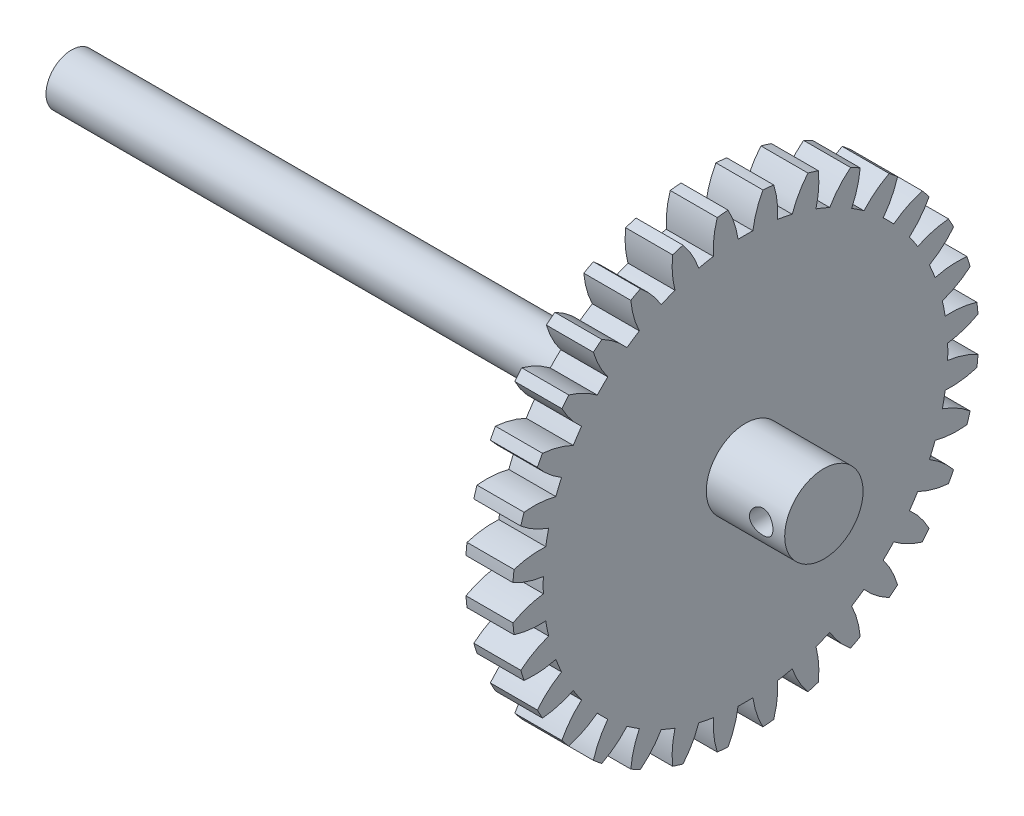
SolidWorks part; units mm, degrees
ref_plane "Plane1" through (0, 0, 0) normal (0, 0, 1) x (1, 0, 0)
ref_plane "Plane2" through (0, 0, 0) normal (0, 1, 0) x (1, 0, 0)
ref_plane "Plane3" through (0, 0, 0) normal (1, 0, 0) x (0, 0, -1)
sketch "HoldingSke" plane through (0, 0, 0) normal (0, 1, 0) x (1, 0, 0)
  line L0 (0, 0) -> (0.4846, -0.3028)
  line L1 (-15, 0) -> (100, 0) construction
  line L2 (0, 0) -> (-2.1039, 2.3779)
  line L3 (0, 0) -> (-11.863, 4.5341)
  line L4 (0, 0) -> (7.3237, 4.5764)
  line L5 (0, 0) -> (-46.8476, -17.4728)
  line L6 (0, 0) -> (-4.9738, -3.3558)
  line L7 (-2.1039, 2.3779) -> (8.6586, 51.2059)
  line L8 (-76.2, 54.61) -> (-76.1, 54.61)
  line L9 (-67.7845, 28.3722) -> (-49.3413, 33.142)
  line L10 (-76.2, 71.12) -> (104.1128, 71.12)
  line L11 (0, 0) -> (-6, 0)
  line L12 (-76.2, 101.6) -> (-76.147, 101.6)
  line L13 (24.9733, 27.94) -> (52.9518, 28.4284)
  line L14 (24.9733, 27.94) -> (24.9743, 27.94)
  line L15 (24.9733, 27.94) -> (100.4006, 29.5858)
  line L16 (-63.627, -1.75) -> (-12.827, -1.75)
  circle A0 centre (0, 0) radius 0.4
  circle A1 centre (0, 0) radius 25.8115
  circle A2 centre (0, 0) radius 37.5
  circle A3 centre (0, 0) radius 0.4
  dimension "MHD" = 51.623
  dimension "Hub_dia" = 75
  dimension "Bore" = 0.8
  dimension "MBD" = 0.8
  dimension "Num_teeth" = 32
  dimension "Pitch" = 0.5714
  dimension "Overall_len" = 50
  dimension "Show_teeth" = 32
  dimension "Thickness" = 6
  dimension "OAL" = 50.0001
  dimension "T_dim" = 0.1
  dimension "Ap" = 14.5
  dimension "H" = 19.05
  dimension "Pitch_radius" = 180.3128
  dimension "Width" = 6
  dimension "Backlash" = 0.053
  dimension "Addendum_fac" = 1
  dimension "Dedendum_fac" = 1.25
  dimension "Clearance_fac" = 0.25
  dimension "Dedendum_add" = 0.001
  dimension "Module" = 1.75
sketch "BasProSke" plane through (0, 0, 0) normal (0, 1, 0) x (1, 0, 0)
  line L0 (-10, 0) -> (60, 0) construction
  line L1 (0, 0) -> (0, 29.75)
  line L2 (0, 0) -> (6, 0)
  line L3 (6, 0) -> (6, 29.75)
  line L4 (6, 29.75) -> (0, 29.75)
  dimension "Thickness" = 6
  dimension "Diameter" = 59.5
revolve "Base-Revolve" add sketch "BasProSke" angle 360 about L0
sketch "TooCutSke" plane through (0, 0, 0) normal (1, 0, 0) x (0, 0, -1)
  line L1 (0, 0) -> (0, 107) construction
  line L2 (0, 0) -> (-1.4666, 27.9616) construction
  line L3 (0, 0) -> (-5.4832, 55.672) construction
  line L4 (-1.4666, 27.9616) -> (-2.7416, 27.836) construction
  arc A0 (0.9481, 25.7941) -> (-0.9481, 25.7941) centre (0, 0) ccw
  arc A1 (2.2372, 29.6912) -> (-2.2372, 29.6912) centre (0, 0) ccw
  circle A2 centre (0, 0) radius 28 construction
  circle A3 centre (0, 0) radius 27.1081 construction
  arc A4 (-0.9481, 25.7941) -> (-2.2372, 29.6912) centre (-12.0459, 24.2847) ccw
  arc A5 (2.2372, 29.6912) -> (0.9481, 25.7941) centre (12.0459, 24.2847) ccw
  dimension "Root_dia" = 51.623
  dimension "Overcut_dia" = 59.5508
  dimension "Pitch_dia" = 56
  dimension "Base_dia" = 54.2163
  dimension "Flank_rad" = 11.2
  dimension "Half_ang" = 5.625
  dimension "Half_CT" = 1.2811
extrude "ToothCut" cut sketch "TooCutSke" along normal through all
fillet "Breaks" [suppressed] radius 0.035
fillet "RootFillets" [suppressed] radius 0.4385
pattern_circular "TeethCuts" count 32 every 11.25 about axis through (-10, 0, 0) along (1, 0, 0) of "ToothCut", "RootFillets", "Breaks"
sketch "HubNeaOneSke" plane through (0, 0, 0) normal (-1, 0, 0) x (0, 0, 1)
  circle A0 centre (0, 0) radius 25.8115
  dimension "Diameter" = 51.623
extrude "HubNearOne" [suppressed] add sketch "HubNeaOneSke" along normal blind 44.0001
sketch "HubNeaBotSke" plane through (0, 0, 0) normal (-1, 0, 0) x (0, 0, 1)
  circle A0 centre (0, 0) radius 25.8115
  dimension "Diameter" = 51.623
extrude "HubNearBoth" [suppressed] add sketch "HubNeaBotSke" along normal blind 22
ref_plane "FarPln" through (6, 0, 0) normal (1, 0, 0) x (0, 0, -1)
sketch "HubFarSke" plane through (6, 0, 0) normal (1, 0, 0) x (0, 0, -1)
  circle A0 centre (0, 0) radius 25.8115
  dimension "Diameter" = 51.623
extrude "HubFar" [suppressed] add sketch "HubFarSke" along normal blind 22
sketch "BorSke" plane through (0, 0, 0) normal (1, 0, 0) x (0, 0, -1)
  circle A0 centre (0, 0) radius 0.4
  dimension "Diameter" = 0.8
extrude "Bore" cut sketch "BorSke" along normal mid plane 100.0001
sketch "KeySke" plane through (0, 0, 0) normal (1, 0, 0) x (0, 0, -1)
  line L0 (-0.05, 0) -> (-0.05, 0.5)
  line L1 (-0.05, 0.5) -> (0.05, 0.5)
  line L2 (0.05, 0.5) -> (0.05, 0)
  line L3 (0, 0) -> (0, 34) construction
  line L4 (-0.05, 0) -> (0.05, 0)
  dimension "Offset" = 0.5
  dimension "Width" = 0.1
extrude "Keyway" [suppressed] cut sketch "KeySke" along normal mid plane 100.0001
pattern_circular "Keyway2" [suppressed] count 2 every 90 about axis through (-10, 0, 0) along (1, 0, 0)
sketch "Sketch1" plane through (6, 0, 0) normal (1, 0, 0) x (0, 0, -1)
  circle A0 centre (0, 0) radius 5
  dimension "D1" = 10
extrude "Boss-Extrude1" add sketch "Sketch1" along normal blind 10
sketch "Sketch2" plane through (0, 0, 0) normal (-1, 0, 0) x (0, 0, 1)
  circle A0 centre (0, 0) radius 3.25
  dimension "D1" = 6.5
extrude "Boss-Extrude2" add sketch "Sketch2" along normal blind 80
sketch "Sketch3" plane through (0, 0, 0) normal (0, 0, 1) x (1, 0, 0)
  line L0 (6, 8.9951) -> (6, 10.7469) construction
  circle A0 centre (13, 0) radius 1.5
  dimension "D2" = 3
  dimension "D1" = 7
extrude "Cut-Extrude1" cut sketch "Sketch3" against normal through all both and the other way through all
sketch "Sketch4" plane through (0, 0, 0) normal (-1, 0, 0) x (0, 0, 1)
  line L0 (0, 0) -> (-61.3585, -18.297) construction
  circle A0 centre (-23.3825, -6.9726) radius 1.725
  dimension "D1" = 3.45
  dimension "D2" = 24.4
extrude "Cut-Extrude2" cut sketch "Sketch4" against normal blind 2.5
equation "' \"Module@HoldingSke\" = 6.35"
equation "' \"Num_teeth@HoldingSke\" = 12"
equation "' \"Ap@HoldingSke\" =  20"
equation "' \"Ap@HoldingSke\" = 20"
equation "' \"Width@HoldingSke\" = 0.5 * 25.4"
equation "' \"Hub_dia@HoldingSke\"= 1 * 25.4"
equation "' \"Hub_dia@HoldingSke\" = 1 * 25.4"
equation "' \"Overall_len@HoldingSke\" = 1.0 * 25.4"
equation "' \"Bore@HoldingSke\" = 0.75 * 25.4"
equation "' \"T_dim@HoldingSke\" = 0.1 * 25.4"
equation "' \"Width@KeySke\" = 0.25 * 25.4"
equation "' \"Show_teeth@HoldingSke\" = 13"
equation "' \"Backlash@HoldingSke\" = 0.009 * 25.4"
equation "' \"Addendum_fac@HoldingSke\" = 1.0"
equation "' \"Dedendum_fac@HoldingSke\" = 1.25"
equation "' \"Dedendum_add@HoldingSke\" = 0.00005 * 25.4"
equation "' \"Clearance_fac@HoldingSke\" = 0.25"
equation "\"Pitch@HoldingSke\" = 1 / \"Module@HoldingSke\""
equation "\"Overcut_dia@TooCutSke\" = (\"Num_teeth@HoldingSke\" + 2 * \"Addendum_fac@HoldingSke\") / \"Pitch@HoldingSke\" + 0.002 * 25.4"
equation "\"Pitch_dia@TooCutSke\" = \"Num_teeth@HoldingSke\" / \"Pitch@HoldingSke\""
equation "\"Base_dia@TooCutSke\" = \"Num_teeth@HoldingSke\" / \"Pitch@HoldingSke\" * cos((\"Ap@HoldingSke\"  * 3.14159265 / 180))"
equation "\"Root_dia@TooCutSke\" = (\"Num_teeth@HoldingSke\" + 2) / \"Pitch@HoldingSke\" - 2 * (\"Addendum_fac@HoldingSke\" + \"Dedendum_fac@HoldingSke\") / \"Pitch@HoldingSke\" - \"Dedendum_add@HoldingSke\" * 2"
equation "\"Half_ang@TooCutSke\" = 180 / \"Num_teeth@HoldingSke\""
equation "\"Half_CT@TooCutSke\" = \"Num_teeth@HoldingSke\" / \"Pitch@HoldingSke\" * sin((3.14159265 / 2 / \"Num_teeth@HoldingSke\")) / 2 - 7 * \"Backlash@HoldingSke\" / 4"
equation "\"Flank_rad@TooCutSke\" = \"Num_teeth@HoldingSke\" / \"Pitch@HoldingSke\" / 5"
equation "\"Radius@RootFillets\" = \"Clearance_fac@HoldingSke\" / \"Pitch@HoldingSke\" + \"Dedendum_add@HoldingSke\""
equation "\"Break_rad@Breaks\" = 0.02 / \"Pitch@HoldingSke\""
equation "\"Thickness@HoldingSke\" = \"Width@HoldingSke\""
equation "\"OAL@HoldingSke\" = \"Thickness@HoldingSke\""
equation "\"MHD@HoldingSke\" = (\"Num_teeth@HoldingSke\" + 2) / \"Pitch@HoldingSke\" - 2 * (\"Addendum_fac@HoldingSke\" + \"Dedendum_fac@HoldingSke\")  / \"Pitch@HoldingSke\" - \"Dedendum_add@HoldingSke\" * 2"
equation "\"MBD@HoldingSke\" = (\"Num_teeth@HoldingSke\" + 2) / \"Pitch@HoldingSke\" - 2 * (\"Addendum_fac@HoldingSke\" + \"Dedendum_fac@HoldingSke\")  / \"Pitch@HoldingSke\" - \"Dedendum_add@HoldingSke\" * 2 - 0.002 * 25.4"
equation "\"MHD@HoldingSke\" = ((sgn( \"MHD@HoldingSke\" - \"Hub_dia@HoldingSke\" )-1)*( \"MHD@HoldingSke\" - \"Hub_dia@HoldingSke\" ))/-2+ \"Hub_dia@HoldingSke\""
equation "\"MBD@HoldingSke\" = ((sgn( \"MBD@HoldingSke\" - \"Bore@HoldingSke\" )-1)*( \"MBD@HoldingSke\" - \"Bore@HoldingSke\" ))/-2+ \"Bore@HoldingSke\""
equation "\"OAL@HoldingSke\" = ((sgn( \"OAL@HoldingSke\" - \"Overall_len@HoldingSke\" )+1)*( \"OAL@HoldingSke\" - \"Overall_len@HoldingSke\" ))/2 + \"Overall_len@HoldingSke\" + 0.000002 * 25.4"
equation "\"Num_teeth@TeethCuts\" = int( \"Show_teeth@HoldingSke\" ) + 1"
equation "\"Num_teeth@TeethCuts\" = ((sgn( \"Num_teeth@TeethCuts\" - \"Num_teeth@HoldingSke\" )-1)*( \"Num_teeth@TeethCuts\" - \"Num_teeth@HoldingSke\" ))/-2+ \"Num_teeth@HoldingSke\""
equation "\"Num_teeth@TeethCuts\" = ((sgn( \"Num_teeth@TeethCuts\" - 2.0)+1)*( \"Num_teeth@TeethCuts\" - 2.0))/2 +2.0"
equation "\"Angle@TeethCuts\" = 360.0 / \"Num_teeth@HoldingSke\""
equation "\"Diameter@BasProSke\" = (\"Num_teeth@HoldingSke\" + 2 * \"Addendum_fac@HoldingSke\") / \"Pitch@HoldingSke\""
equation "\"Thickness@BasProSke\"  = \"Thickness@HoldingSke\""
equation "' \"Fillet_rad@BasProSke\" =  \"Thickness@HoldingSke\" * 0.05"
equation "' \"Fillet_rad@BasProSke\" = \"Thickness@HoldingSke\" * 0.05"
equation "\"MHD@HoldingSke\" = ((sgn( \"MHD@HoldingSke\" - \"Root_dia@TooCutSke\" )-1)*( \"MHD@HoldingSke\" - \"Root_dia@TooCutSke\" ))/-2+ \"Root_dia@TooCutSke\""
equation "\"Diameter@HubNeaOneSke\" = \"MHD@HoldingSke\""
equation "\"Length@HubNearOne\" = \"OAL@HoldingSke\" - \"Thickness@BasProSke\""
equation "\"Diameter@HubNeaBotSke\" = \"MHD@HoldingSke\""
equation "\"Length@HubNearBoth\" = ( \"OAL@HoldingSke\" - \"Thickness@BasProSke\" ) / 2.0"
equation "\"Thickness@FarPln\" = \"Thickness@BasProSke\""
equation "\"Diameter@HubFarSke\" = \"MHD@HoldingSke\""
equation "\"Length@HubFar\" = ( \"OAL@HoldingSke\" - \"Thickness@BasProSke\" ) / 2.0"
equation "\"Diameter@BorSke\" = \"MBD@HoldingSke\""
equation "\"D1@Bore\" = \"OAL@HoldingSke\" * 2.0"
equation "\"D1@Keyway\" = \"OAL@HoldingSke\" * 2.0"
equation "\"Offset@KeySke\" = \"T_dim@HoldingSke\" + \"MBD@HoldingSke\" / 2.0"
